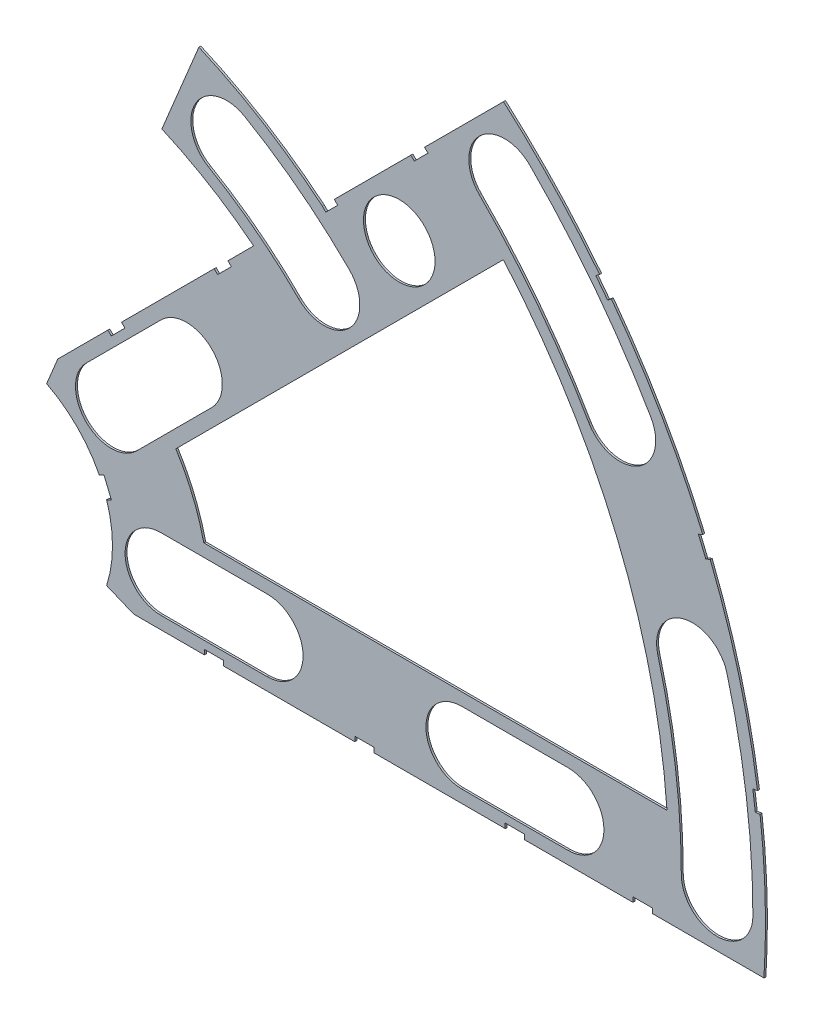
SolidWorks part; units mm, degrees
material "PTFE (general)"
ref_plane "Front Plane" through (0, 0, 0) normal (0, 0, 1) x (1, 0, 0)
ref_plane "Top Plane" through (0, 0, 0) normal (0, 1, 0) x (1, 0, 0)
ref_plane "Right Plane" through (0, 0, 0) normal (1, 0, 0) x (0, 0, -1)
sketch "Sketch1" plane through (0, 0, 0) normal (0, 0, 1) x (1, 0, 0)
  line L0 (0, 0) -> (320.3893, 0) construction
  line L1 (0, 0) -> (155.5285, 155.5285) construction
  line L2 (27.2188, 62.3934) -> (22.3577, 50.6576)
  line L3 (8.6967, 17.6769) -> (7.229, 14.1336)
  line L4 (101.4014, -6.35) -> (18.6489, -6.35)
  line L5 (15.1056, -4.8823) -> (18.6489, -6.35)
  line L6 (88.6729, 6.35) -> (27.8605, 6.35)
  line L7 (67.2115, 76.1917) -> (43.4342, 52.4144)
  line L8 (34.4055, 43.3857) -> (8.6967, 17.6769)
  line L9 (67.1914, 58.2111) -> (24.1905, 15.2102)
  line L10 (0, 0) -> (40.4486, 97.6516) construction
  line L11 (0, 0) -> (123.4567, -51.1374) construction
  line L18 (8.6967, 17.6769) -> (13.294, 8.6183) construction
  line L19 (18.6489, -6.35) -> (15.4943, 3.3063) construction
  line L20 (27.8605, 6.35) -> (27.7442, 6.7059) construction
  line L21 (24.1905, 15.2102) -> (24.3599, 14.8764) construction
  line L22 (67.2115, 76.1917) -> (8.6967, 17.6769) construction
  arc A0 (7.229, 14.1336) -> (15.1056, -4.8823) centre (0, 0) cw
  arc A1 (67.2115, 76.1917) -> (101.4014, -6.35) centre (0, 0) cw
  arc A2 (24.1905, 15.2102) -> (27.8605, 6.35) centre (0, 0) cw
  arc A3 (67.1914, 58.2111) -> (88.6729, 6.35) centre (0, 0) cw
  arc A4 (27.2188, 62.3934) -> (43.4342, 52.4144) centre (0, 0) cw
  arc A5 (22.3577, 50.6576) -> (34.4055, 43.3857) centre (0, 0) cw
  arc A8 (13.294, 8.6183) -> (15.4943, 3.3063) centre (0, 0) cw construction
  arc A9 (24.3599, 14.8764) -> (27.7442, 6.7059) centre (0, 0) cw construction
  dimension "D1" = 45
  dimension "D3" = 6.35
  dimension "D4" = 15.875
  dimension "D7" = 22.5
  dimension "D8" = 101.6
  dimension "D11" = 12.7
  dimension "D12" = 12.7
  dimension "D2" = 55.372
  dimension "D13" = 12.7
  dimension "D5" = 67.5
  dimension "D9" = 1.27
  dimension "D10" = 1.27
  dimension "D14" = 6.35
  dimension "D15" = 6.35
  dimension "D16" = 1.27
  dimension "D6" = 12.7
extrude "Boss-Extrude1" add sketch "Sketch1" along normal blind 0.254
sketch "Sketch2" plane through (0, 0, 0.254) normal (0, 0, 1) x (1, 0, 0)
  line L0 (0, 0) -> (101.6, 0) construction
  line L1 (0, 0) -> (71.842, 71.842) construction
  line L2 (0, 0) -> (30.861, 53.4528) construction
  line L3 (0, 0) -> (22.225, 0) construction
  line L4 (0, 0) -> (15.7154, 15.7154) construction
  line L5 (0, 0) -> (95.25, 0) construction
  line L6 (0, 0) -> (92.0044, 24.6525) construction
  arc A0 (101.4014, -6.35) -> (67.2115, 76.1917) centre (0, 0) ccw construction
  circle A1 centre (22.225, 0) radius 4.699
  arc A2 (15.1056, -4.8823) -> (7.229, 14.1336) centre (0, 0) ccw construction
  circle A3 centre (36.195, 0) radius 4.699
  circle A4 centre (61.722, 0) radius 4.699
  circle A5 centre (75.692, 0) radius 4.699
  circle A6 centre (95.25, 0) radius 4.699
  circle A7 centre (15.7154, 15.7154) radius 4.699
  circle A8 centre (25.5937, 25.5937) radius 4.699
  circle A9 centre (43.644, 43.644) radius 4.699
  circle A10 centre (53.5223, 53.5223) radius 4.699
  circle A11 centre (92.0044, 24.6525) radius 4.699
  circle A12 centre (82.4889, 47.625) radius 4.699
  circle A13 centre (67.3519, 67.3519) radius 4.699
  circle A14 centre (30.861, 53.4528) radius 4.699
  arc A15 (43.4342, 52.4144) -> (27.2188, 62.3934) centre (0, 0) ccw construction
  dimension "D3" = 9.398
  dimension "D1" = 45
  dimension "D2" = 6.35
  dimension "D4" = 6.35
  dimension "D5" = 13.97
  dimension "D7" = 13.97
  dimension "D8" = 19.558
  dimension "D9" = 45
  dimension "D10" = 15
  dimension "D11" = 15
  dimension "D12" = 6.35
  dimension "D6" = 25.527
  dimension "D13" = 2
extrude "Cut-Extrude1" cut sketch "Sketch2" against normal through all
sketch "Sketch3" plane through (0, 0, 0.254) normal (0, 0, 1) x (1, 0, 0)
  line L0 (15.2664, 24.2467) -> (17.0625, 26.0427)
  line L1 (15.2664, 24.2467) -> (15.7154, 23.7977)
  line L2 (17.0625, 26.0427) -> (17.5115, 25.5937)
  line L3 (15.7154, 23.7977) -> (17.5115, 25.5937)
  line L5 (43.4342, 52.4144) -> (44.9911, 53.9713)
  line L6 (43.4342, 52.4144) -> (43.8832, 51.9654)
  line L7 (44.9911, 53.9713) -> (45.4401, 53.5223)
  line L8 (43.8832, 51.9654) -> (45.4401, 53.5223)
  line L9 (27.94, -6.35) -> (30.48, -6.35)
  line L10 (27.94, -6.35) -> (27.94, -5.715)
  line L11 (30.48, -6.35) -> (30.48, -5.715)
  line L12 (27.94, -5.715) -> (30.48, -5.715)
  line L13 (18.6489, -6.35) -> (101.4014, -6.35) construction
  line L14 (67.437, -6.35) -> (69.977, -6.35)
  line L15 (67.437, -6.35) -> (67.437, -5.715)
  line L16 (69.977, -6.35) -> (69.977, -5.715)
  line L17 (67.437, -5.715) -> (69.977, -5.715)
  line L18 (29.2307, 38.211) -> (31.0268, 40.007)
  line L19 (29.2307, 38.211) -> (29.6797, 37.762)
  line L20 (31.0268, 40.007) -> (31.4758, 39.558)
  line L21 (29.6797, 37.762) -> (31.4758, 39.558)
  line L22 (56.845, 65.8253) -> (55.049, 64.0292)
  line L23 (56.845, 65.8253) -> (57.294, 65.3763)
  line L24 (55.049, 64.0292) -> (55.498, 63.5802)
  line L25 (57.294, 65.3763) -> (55.498, 63.5802)
  line L26 (47.6885, -6.35) -> (50.2285, -6.35)
  line L27 (47.6885, -6.35) -> (47.6885, -5.715)
  line L28 (50.2285, -6.35) -> (50.2285, -5.715)
  line L29 (47.6885, -5.715) -> (50.2285, -5.715)
  line L30 (84.201, -6.35) -> (86.741, -6.35)
  line L31 (84.201, -6.35) -> (84.201, -5.715)
  line L32 (86.741, -6.35) -> (86.741, -5.715)
  line L33 (84.201, -5.715) -> (86.741, -5.715)
  line L34 (0, 0) -> (100.7308, 13.2615) construction
  line L35 (0, 0) -> (93.8662, 38.8806) construction
  line L36 (0, 0) -> (80.6047, 61.8502) construction
  line L37 (0, 0) -> (101.6, 0) construction
  line L38 (99.9355, 14.4377) -> (100.267, 11.9194)
  line L39 (99.9355, 14.4377) -> (101.1946, 14.6035)
  line L40 (100.267, 11.9194) -> (101.5261, 12.0852)
  line L41 (101.1946, 14.6035) -> (101.5261, 12.0852)
  line L42 (99.9355, 14.4377) -> (101.5261, 12.0852) construction
  line L43 (100.267, 11.9194) -> (101.1946, 14.6035) construction
  line L44 (93.7655, 37.4643) -> (94.9388, 37.9503)
  line L45 (93.7655, 37.4643) -> (92.7935, 39.811)
  line L46 (94.9388, 37.9503) -> (93.9668, 40.297)
  line L47 (92.7935, 39.811) -> (93.9668, 40.297)
  line L48 (93.7655, 37.4643) -> (93.9668, 40.297) construction
  line L49 (94.9388, 37.9503) -> (92.7935, 39.811) construction
  line L50 (79.3278, 62.4712) -> (80.874, 60.456)
  line L51 (79.3278, 62.4712) -> (80.3354, 63.2443)
  line L52 (80.874, 60.456) -> (81.8816, 61.2292)
  line L53 (80.3354, 63.2443) -> (81.8816, 61.2292)
  line L54 (79.3278, 62.4712) -> (81.8816, 61.2292) construction
  line L55 (80.874, 60.456) -> (80.3354, 63.2443) construction
  line L56 (13.5939, 7.0054) -> (14.5659, 4.6588)
  line L57 (13.5939, 7.0054) -> (14.7672, 7.4914)
  line L58 (14.5659, 4.6588) -> (15.7393, 5.1448)
  line L59 (14.7672, 7.4914) -> (15.7393, 5.1448)
  line L60 (13.5939, 7.0054) -> (15.7393, 5.1448) construction
  line L61 (14.5659, 4.6588) -> (14.7672, 7.4914) construction
  line L62 (34.4055, 43.3857) -> (8.6967, 17.6769) construction
  line L63 (67.2115, 76.1917) -> (43.4342, 52.4144) construction
  circle A0 centre (15.7154, 15.7154) radius 4.699 construction
  circle A1 centre (53.5223, 53.5223) radius 4.699 construction
  circle A2 centre (22.225, 0) radius 4.699 construction
  circle A3 centre (61.722, 0) radius 4.699 construction
  arc A4 (101.4014, -6.35) -> (67.2115, 76.1917) centre (0, 0) ccw construction
  arc A9 (15.1056, -4.8823) -> (7.229, 14.1336) centre (0, 0) ccw construction
  circle A10 centre (36.195, 0) radius 4.699 construction
  circle A11 centre (75.692, 0) radius 4.699 construction
  circle A12 centre (53.5223, 53.5223) radius 4.699 construction
  circle A13 centre (25.5937, 25.5937) radius 4.699 construction
  point P75 (14.6666, 6.0751)
  dimension "D2" = 5.715
  dimension "D3" = 2.54
  dimension "D8" = 0.635
  dimension "D9" = 5.715
  dimension "D12" = 5.715
  dimension "D4" = 7.5
  dimension "D5" = 22.5
  dimension "D7" = 37.5
  dimension "D10" = 90
  dimension "D11" = 1.27
  dimension "D14" = 0.635
  dimension "D15" = 90
  dimension "D18" = 0.635
  dimension "D19" = 90
  dimension "D22" = 0.635
  dimension "D20" = 1.27
  dimension "D17" = 0.635
  dimension "D21" = 5.715
  dimension "D13" = 11.4935
  dimension "D16" = 8.509
  dimension "D23" = 8.509
  dimension "D24" = 11.4935
extrude "Cut-Extrude2" cut sketch "Sketch3" against normal through all
sketch "Sketch7" plane through (0, 0, 0.254) normal (0, 0, 1) x (1, 0, 0)
  line L0 (15.7154, 15.7154) -> (25.5937, 25.5937) construction
  line L1 (12.3928, 19.0381) -> (22.271, 28.9164)
  line L2 (19.0381, 12.3928) -> (28.9164, 22.271)
  line L3 (22.225, 0) -> (36.195, 0) construction
  line L4 (22.225, 4.699) -> (36.195, 4.699)
  line L5 (22.225, -4.699) -> (36.195, -4.699)
  line L6 (61.722, 0) -> (75.692, 0) construction
  line L7 (61.722, 4.699) -> (75.692, 4.699)
  line L8 (61.722, -4.699) -> (75.692, -4.699)
  arc A0 (43.644, 43.644) -> (30.861, 53.4528) centre (0, 0) ccw construction
  arc A1 (46.9667, 46.9667) -> (33.2105, 57.5223) centre (0, 0) ccw
  arc A2 (40.3213, 40.3213) -> (28.5115, 49.3834) centre (0, 0) ccw
  arc A3 (40.3213, 40.3213) -> (46.9667, 46.9667) centre (43.644, 43.644) ccw
  arc A4 (33.2105, 57.5223) -> (28.5115, 49.3834) centre (30.861, 53.4528) ccw
  circle A5 centre (30.861, 53.4528) radius 4.699 construction
  circle A6 centre (43.644, 43.644) radius 4.699 construction
  arc A7 (12.3928, 19.0381) -> (19.0381, 12.3928) centre (15.7154, 15.7154) ccw
  arc A8 (28.9164, 22.271) -> (22.271, 28.9164) centre (25.5937, 25.5937) ccw
  arc A9 (22.225, 4.699) -> (22.225, -4.699) centre (22.225, 0) ccw
  arc A10 (36.195, -4.699) -> (36.195, 4.699) centre (36.195, 0) ccw
  arc A11 (61.722, 4.699) -> (61.722, -4.699) centre (61.722, 0) ccw
  arc A12 (75.692, -4.699) -> (75.692, 4.699) centre (75.692, 0) ccw
  arc A13 (95.25, 0) -> (92.0044, 24.6525) centre (0, 0) ccw construction
  arc A14 (99.949, 0) -> (96.5433, 25.8687) centre (0, 0) ccw
  arc A15 (90.551, 0) -> (87.4655, 23.4363) centre (0, 0) ccw
  arc A16 (90.551, 0) -> (99.949, 0) centre (95.25, 0) ccw
  arc A17 (96.5433, 25.8687) -> (87.4655, 23.4363) centre (92.0044, 24.6525) ccw
  arc A18 (82.4889, 47.625) -> (67.3519, 67.3519) centre (0, 0) ccw construction
  arc A19 (86.5584, 49.9745) -> (70.6746, 70.6746) centre (0, 0) ccw
  arc A20 (78.4195, 45.2755) -> (64.0292, 64.0292) centre (0, 0) ccw
  arc A21 (78.4195, 45.2755) -> (86.5584, 49.9745) centre (82.4889, 47.625) ccw
  arc A22 (70.6746, 70.6746) -> (64.0292, 64.0292) centre (67.3519, 67.3519) ccw
  circle A23 centre (92.0044, 24.6525) radius 4.699 construction
  circle A24 centre (67.3519, 67.3519) radius 4.699 construction
  circle A25 centre (82.4889, 47.625) radius 4.699 construction
  circle A26 centre (95.25, 0) radius 4.699 construction
  circle A27 centre (75.692, 0) radius 4.699 construction
  circle A28 centre (61.722, 0) radius 4.699 construction
  circle A29 centre (36.195, 0) radius 4.699 construction
  circle A30 centre (22.225, 0) radius 4.699 construction
  circle A31 centre (25.5937, 25.5937) radius 4.699 construction
  circle A32 centre (15.7154, 15.7154) radius 4.699 construction
  point P5 (37.574, 48.9674)
  point P18 (20.6546, 20.6546)
  point P23 (29.21, 0)
  point P32 (68.707, 0)
  point P46 (94.4351, 12.4326)
  point P51 (75.5669, 57.9845)
  dimension "D1" = 9.398
  dimension "D2" = 9.398
  dimension "D3" = 9.398
  dimension "D4" = 9.398
  dimension "D5" = 9.398
  dimension "D6" = 9.398
extrude "Cut-Extrude3" cut sketch "Sketch7" against normal through all
equation "\"LayerThick\"=0.01"
equation "\"D1@Boss-Extrude1\"=\"LayerThick\""
equation "\"CoilSep\"= 1.005"
equation "\"D6@Sketch2\"=\"CoilSep\""
equation "\"CoilSep2\"= \"D8@Sketch2\""
equation "\"D13@Sketch3\"=\"CoilSep\"/2-.05"
equation "\"D16@Sketch3\"=\"CoilSep2\"/2-.05"
equation "\"D23@Sketch3\"=\"CoilSep2\"/2-.05"
equation "\"D24@Sketch3\"=\"CoilSep\"/2-.05"
